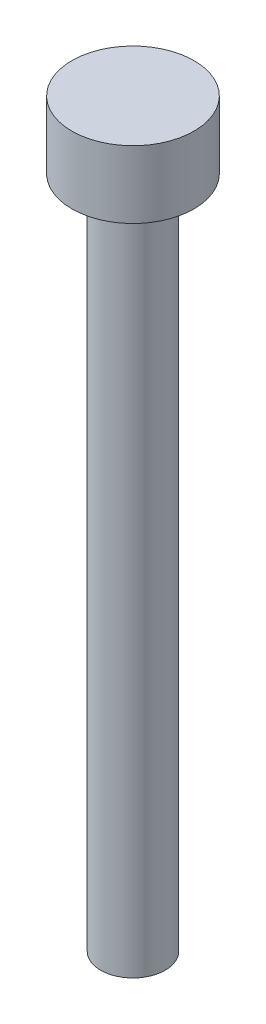
SolidWorks part; units mm, degrees
ref_plane "Front Plane" through (0, 0, 0) normal (0, 0, 1) x (1, 0, 0)
ref_plane "Top Plane" through (0, 0, 0) normal (0, 1, 0) x (1, 0, 0)
ref_plane "Right Plane" through (0, 0, 0) normal (1, 0, 0) x (0, 0, -1)
sketch "Sketch1" plane through (0, 0, 0) normal (0, 1, 0) x (1, 0, 0)
  circle A0 centre (0, 0) radius 2.72
  dimension "D1" = 5.44
extrude "Boss-Extrude1" add sketch "Sketch1" along normal blind 3
sketch "Sketch2" plane through (0, 0, 0) normal (0, -1, 0) x (1, 0, 0)
  circle A0 centre (0, 0) radius 1.44
  dimension "D1" = 2.88
extrude "Boss-Extrude2" add sketch "Sketch2" along normal blind 30
